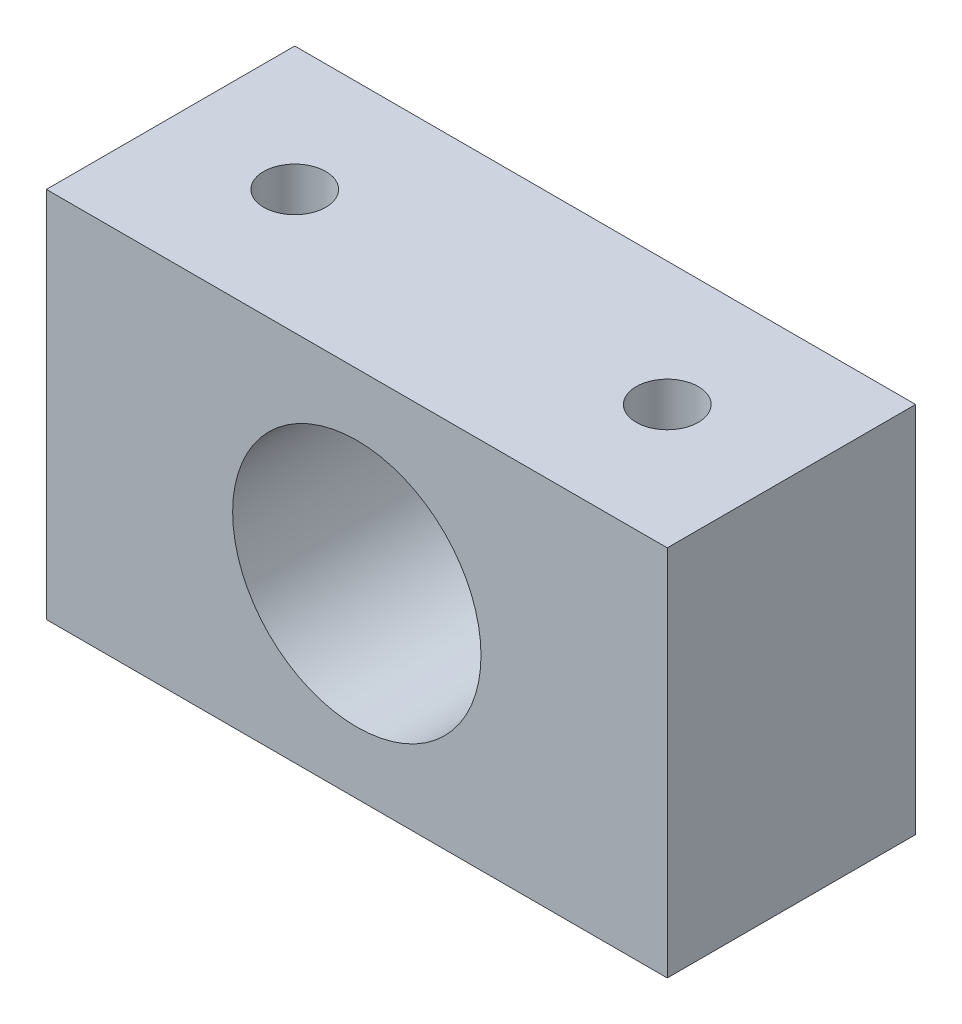
SolidWorks part; units mm, degrees
ref_plane "Front Plane" through (0, 0, 0) normal (0, 0, 1) x (1, 0, 0)
ref_plane "Top Plane" through (0, 0, 0) normal (0, 1, 0) x (1, 0, 0)
ref_plane "Right Plane" through (0, 0, 0) normal (1, 0, 0) x (0, 0, -1)
sketch "Sketch1" plane through (0, 0, 0) normal (0, 0, 1) x (1, 0, 0)
  line L1 (15.875, 9.525) -> (-15.875, 9.525)
  line L2 (15.875, 9.525) -> (15.875, -9.525)
  line L3 (15.875, -9.525) -> (-15.875, -9.525)
  line L4 (-15.875, 9.525) -> (-15.875, -9.525)
  line L5 (15.875, 9.525) -> (-15.875, -9.525) construction
  line L6 (15.875, -9.525) -> (-15.875, 9.525) construction
  point P0 (0, 0)
  dimension "D1" = 31.75
  dimension "D2" = 19.05
extrude "Boss-Extrude1" add sketch "Sketch1" along normal blind 12.7
sketch "Sketch2" plane through (0, 0, 12.7) normal (0, 0, 1) x (1, 0, 0)
  circle A0 centre (0, 0) radius 6.35
  dimension "D1" = 12.7
extrude "Cut-Extrude1" cut sketch "Sketch2" against normal blind 12.7
sketch "Sketch3" plane through (0, 9.525, 0) normal (0, 1, 0) x (1, 0, 0)
  line L0 (-9.525, -6.35) -> (9.525, -6.35) construction
  line L1 (-3.1243, 0) -> (-3.1243, -12.7) construction
  line L2 (15.875, 0) -> (-15.875, 0) construction
  line L3 (15.875, -12.7) -> (-15.875, -12.7) construction
  line L4 (-15.875, -12.7) -> (-15.875, 0) construction
  circle A0 centre (-9.525, -6.35) radius 1.5875
  circle A1 centre (9.525, -6.35) radius 1.5875
  point P4 (0, -6.35)
  point P12 (-3.1243, -6.35)
  point P13 (-10.5445, -6.35)
  dimension "D1" = 3.175
  dimension "D2" = 6.35
extrude "Cut-Extrude2" cut sketch "Sketch3" against normal blind 12.7
